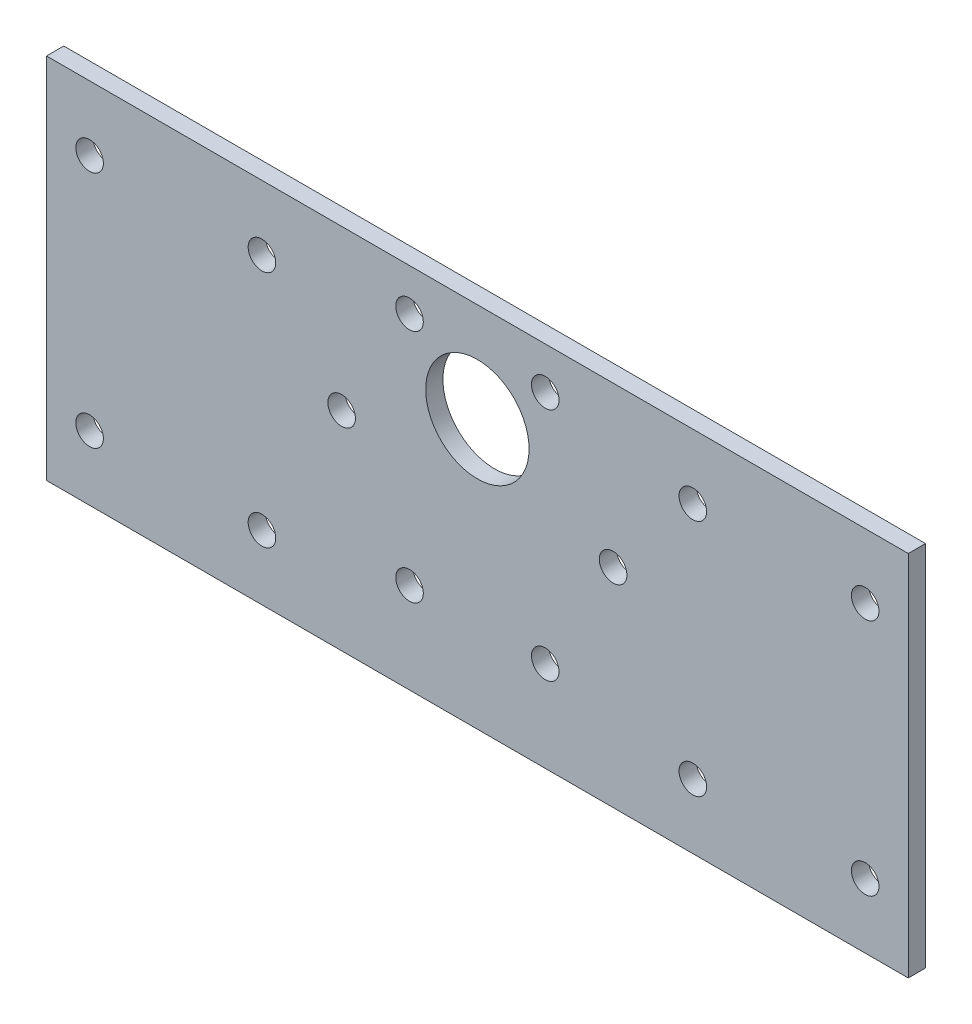
SolidWorks part; units mm, degrees
ref_plane "正面" through (0, 0, 0) normal (0, 0, 1) x (1, 0, 0)
ref_plane "平面" through (0, 0, 0) normal (0, 1, 0) x (1, 0, 0)
ref_plane "右側面" through (0, 0, 0) normal (1, 0, 0) x (0, 0, -1)
sketch "ｽｹｯﾁ1" plane through (0, 0, 0) normal (0, 0, 1) x (1, 0, 0)
  line L0 (0, 0) -> (15.75, 0)
  line L1 (-50, 25) -> (50, 25)
  line L2 (-50, 25) -> (-50, -25)
  line L3 (-50, -25) -> (50, -25)
  line L4 (50, 25) -> (50, -25)
  line L5 (-50, 25) -> (50, -25) construction
  line L6 (-50, -25) -> (50, 25) construction
  line L7 (0, 0) -> (-15.75, 0)
  line L8 (0, 0) -> (0, 6.5)
  line L9 (0, 6.5) -> (15.75, 6.5)
  line L10 (0, 6.5) -> (-15.75, 6.5)
  circle A0 centre (15.75, 0) radius 1.6
  circle A1 centre (-15.75, 0) radius 1.6
  circle A2 centre (-15.75, 6.5) radius 1.6
  circle A3 centre (15.75, 6.5) radius 1.6
  point P0 (0, 0)
  dimension "D5" = 3.2
  dimension "D6" = 3.2
  dimension "D10" = 3.2
  dimension "D11" = 3.2
  dimension "D1" = 100
  dimension "D2" = 50
  dimension "D3" = 15.75
  dimension "D4" = 15.75
  dimension "D7" = 6.5
  dimension "D8" = 15.75
  dimension "D9" = 15.75
extrude "ﾎﾞｽ - 押し出し1" add sketch "ｽｹｯﾁ1" along normal blind 2
sketch "ｽｹｯﾁ2" plane through (0, 0, 2) normal (0, 0, 1) x (1, 0, 0)
  line L0 (0, 25) -> (0, 14.5)
  line L1 (-50, 25) -> (50, 25) construction
  line L2 (0, 14.5) -> (15.75, 14.5)
  line L3 (0, 14.5) -> (-15.75, 14.5)
  line L4 (0, -25) -> (0, -14.5)
  line L5 (-50, -25) -> (50, -25) construction
  line L6 (0, -14.5) -> (15.75, -14.5)
  line L7 (0, -14.5) -> (-15.75, -14.5)
  circle A0 centre (-15.75, 14.5) radius 1.6
  circle A1 centre (15.75, 14.5) radius 1.6
  circle A2 centre (-15.75, -14.5) radius 1.6
  circle A3 centre (15.75, -14.5) radius 1.6
  dimension "D2" = 3.2
  dimension "D3" = 3.2
  dimension "D5" = 3.2
  dimension "D6" = 3.2
  dimension "D1" = 10.5
  dimension "D4" = 10.5
  dimension "D7" = 15.75
  dimension "D8" = 15.75
  dimension "D9" = 15.75
  dimension "D10" = 15.75
sketch "ｽｹｯﾁ3" plane through (0, 0, 2) normal (0, 0, 1) x (1, 0, 0)
  line L0 (-15.75, 6.5) -> (0, 6.5)
  line L1 (0, 6.5) -> (0, 13.5)
  circle A0 centre (0, 13.5) radius 6
  dimension "D3" = 12
  dimension "D1" = 7
  dimension "D2" = 15.75
extrude "ｶｯﾄ - 押し出し2" cut sketch "ｽｹｯﾁ3" against normal blind 2
sketch "ｽｹｯﾁ4" plane through (0, 0, 2) normal (0, 0, 1) x (1, 0, 0)
  line L0 (15.75, 6.5) -> (0, 6.5)
  line L1 (0, 6.5) -> (7.875, 20.1399)
  line L2 (0, 6.5) -> (-15.75, 6.5)
  line L3 (0, 6.5) -> (-7.875, 20.1399)
  line L4 (0, 6.5) -> (7.875, -7.1399)
  line L5 (0, 6.5) -> (-7.875, -7.1399)
  circle A0 centre (-7.875, 20.1399) radius 1.6
  circle A1 centre (7.875, 20.1399) radius 1.6
  circle A2 centre (-7.875, -7.1399) radius 1.6
  circle A3 centre (7.875, -7.1399) radius 1.6
  dimension "D7" = 3.2
  dimension "D8" = 3.2
  dimension "D9" = 3.2
  dimension "D10" = 3.2
  dimension "D13" = 15.75
  dimension "D1" = 15.75
  dimension "D2" = 60
  dimension "D3" = 15.75
  dimension "D4" = 15.75
  dimension "D5" = 60
  dimension "D6" = 15.75
  dimension "D11" = 60
  dimension "D12" = 60
  dimension "D14" = 15.75
extrude "ｶｯﾄ - 押し出し3" cut sketch "ｽｹｯﾁ4" against normal blind 2
sketch "ｽｹｯﾁ5" plane through (0, 0, 2) normal (0, 0, 1) x (1, 0, 0)
  line L2 (0, 0) -> (0, -10.16)
  line L3 (0, -10.16) -> (25, -10.16)
  line L4 (0, -10.16) -> (-25, -10.16)
  line L5 (-25, -10.16) -> (-45, -10.16)
  line L6 (-45, -10.16) -> (-50, -10.16)
  line L7 (-50, 25) -> (-50, -25) construction
  line L8 (25, -10.16) -> (45, -10.16)
  line L9 (45, -10.16) -> (50, -10.16)
  line L10 (50, 25) -> (50, -25) construction
  circle A0 centre (-25, -10.16) radius 1.6
  circle A1 centre (25, -10.16) radius 1.6
  circle A2 centre (45, -10.16) radius 1.6
  circle A3 centre (-45, -10.16) radius 1.6
  dimension "D2" = 3.2
  dimension "D3" = 3.2
  dimension "D8" = 3.2
  dimension "D9" = 3.2
  dimension "D1" = 10.16
  dimension "D4" = 5
  dimension "D5" = 5
  dimension "D6" = 20
  dimension "D7" = 20
extrude "ｶｯﾄ - 押し出し7" cut sketch "ｽｹｯﾁ5" against normal through all contours L5 A3 L6 | L6 A3 L5 | L4 A0 L5 | L5 A0 L4 | L9 A2 L8 | L8 A2 L9 | L8 A1 L3 | L3 A1 L8
sketch "ｽｹｯﾁ6" plane through (0, -25, 0) normal (0, -1, 0) x (1, 0, 0)
  line L1 (-50, 2) -> (50, 2)
  line L2 (-50, 2) -> (-50, 0)
  line L3 (-50, 0) -> (50, 0)
  line L4 (50, 2) -> (50, 0)
extrude "ｶｯﾄ - 押し出し8" cut sketch "ｽｹｯﾁ6" against normal blind 7.34
sketch "ｽｹｯﾁ7" plane through (0, 0, 2) normal (0, 0, 1) x (1, 0, 0)
  line L0 (-50, 25) -> (-50, 17.5)
  line L1 (-50, 25) -> (-50, -17.66) construction
  line L2 (-50, 17.5) -> (-45, 17.5)
  line L3 (-45, 17.5) -> (-25, 17.5)
  line L4 (50, 25) -> (50, 17.5)
  line L5 (50, 25) -> (50, -17.66) construction
  line L6 (50, 17.5) -> (45, 17.5)
  line L7 (45, 17.5) -> (25, 17.5)
  circle A0 centre (-45, 17.5) radius 1.6
  circle A1 centre (-25, 17.5) radius 1.6
  circle A2 centre (45, 17.5) radius 1.6
  circle A3 centre (25, 17.5) radius 1.6
  dimension "D3" = 3.2
  dimension "D4" = 3.2
  dimension "D9" = 3.2
  dimension "D10" = 3.2
  dimension "D1" = 5
  dimension "D2" = 20
  dimension "D5" = 7.5
  dimension "D6" = 7.5
  dimension "D7" = 5
  dimension "D8" = 20
extrude "ｶｯﾄ - 押し出し9" cut sketch "ｽｹｯﾁ7" against normal blind 10
